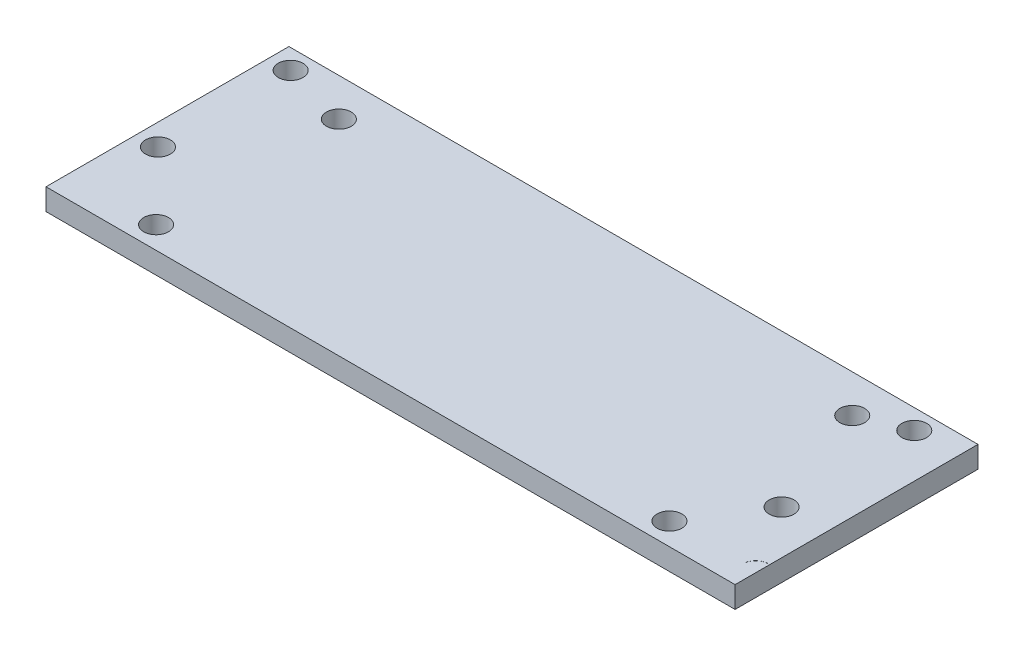
SolidWorks part; units mm, degrees
ref_plane "Front" through (0, 0, 0) normal (0, 0, 1) x (1, 0, 0)
ref_plane "Top" through (0, 0, 0) normal (0, 1, 0) x (1, 0, 0)
ref_plane "Right" through (0, 0, 0) normal (1, 0, 0) x (0, 0, -1)
sketch "Sketch1" plane through (0, 0, 0) normal (0, 1, 0) x (1, 0, 0)
  line L1 (57.15, -17.907) -> (-57.15, -17.907)
  line L2 (57.15, -17.907) -> (57.15, 17.907)
  line L3 (57.15, 17.907) -> (-57.15, 17.907)
  line L4 (-57.15, -17.907) -> (-57.15, 17.907)
  line L5 (57.15, -17.907) -> (-57.15, 17.907) construction
  line L6 (57.15, 17.907) -> (-57.15, -17.907) construction
  point P0 (0, 0)
  dimension "D1" = 35.814
  dimension "D2" = 114.3
extrude "Boss-Extrude1" add sketch "Sketch1" along normal blind 3.175
sketch "Sketch3" plane through (0, 3.175, 0) normal (0, 1, 0) x (1, 0, 0)
  line L0 (0, 17.907) -> (0, -17.907) construction
  line L1 (57.15, 17.907) -> (-57.15, 17.907) construction
  line L2 (-57.15, -17.907) -> (57.15, -17.907) construction
  line L3 (-37.592, 17.907) -> (-50.8, 17.907) construction
  line L4 (-50.8, 17.907) -> (-57.15, 17.907) construction
  line L5 (-53.975, 17.907) -> (-53.975, 14.986) construction
  line L6 (-53.975, 14.986) -> (-53.975, -4.572) construction
  line L7 (-50.8, 17.907) -> (-37.592, 17.907) construction
  line L8 (-44.196, 17.907) -> (-44.196, 12.319) construction
  line L9 (-44.196, 12.319) -> (-44.196, -14.6304) construction
  circle A0 centre (-53.975, 14.986) radius 1.8288
  circle A1 centre (-53.975, -4.572) radius 1.8288
  circle A2 centre (-44.196, 12.319) radius 1.8288
  circle A3 centre (-44.196, -14.6304) radius 1.8288
  circle A4 centre (44.196, -14.6304) radius 1.8288
  circle A5 centre (53.975, -4.572) radius 1.8288
  circle A6 centre (44.196, 12.319) radius 1.8288
  circle A7 centre (53.975, 14.986) radius 1.8288
  dimension "D3" = 3.6576
  dimension "D5" = 3.6576
  dimension "D7" = 3.6576
  dimension "D9" = 26.9494
  dimension "D10" = 3.6576
  dimension "D1" = 50.8
  dimension "D2" = 2.921
  dimension "D4" = 19.558
  dimension "D6" = 13.208
  dimension "D8" = 5.588
extrude "Cut-Extrude2" cut sketch "Sketch3" against normal through all
sketch "Sketch4" plane through (0, 3.175, 0) normal (0, 1, 0) x (1, 0, 0)
  line L0 (57.15, 17.907) -> (-57.15, 17.907) construction
  line L1 (57.15, -17.907) -> (44.45, -17.907)
  line L2 (57.15, -17.907) -> (57.15, 17.907)
  line L3 (57.15, 17.907) -> (44.45, 17.907)
  line L4 (44.45, -17.907) -> (44.45, 17.907)
  dimension "D1" = 12.7
extrude "Cut-Extrude3" cut sketch "Sketch4" against normal through all
sketch "Sketch5" plane through (0, 3.175, 0) normal (0, 1, 0) x (1, 0, 0)
  line L0 (-6.35, 17.907) -> (-6.35, -17.907) construction
  line L1 (44.45, 17.907) -> (-57.15, 17.907) construction
  line L2 (-57.15, -17.907) -> (44.45, -17.907) construction
  circle A0 centre (-44.196, 12.319) radius 1.8288
  circle A1 centre (-53.975, 14.986) radius 1.8288
  circle A2 centre (-53.975, -4.572) radius 1.8288
  circle A3 centre (-44.196, -14.6304) radius 1.8288
  circle A4 centre (31.496, -14.6304) radius 1.8288
  circle A5 centre (41.275, -4.572) radius 1.8288
  circle A6 centre (31.496, 12.319) radius 1.8288
  circle A7 centre (41.275, 14.986) radius 1.8288
extrude "Cut-Extrude4" cut sketch "Sketch5" against normal through all
sketch "Sketch6" plane through (0, 3.175, 0) normal (0, 1, 0) x (1, 0, 0)
  line L0 (44.196, -16.4592) -> (44.45, -16.7132)
  line L1 (44.45, -16.4415) -> (44.45, -17.907) construction
  line L2 (44.45, -16.7132) -> (44.45, -12.5512)
  line L3 (44.45, 10.5079) -> (44.45, -12.8193) construction
  line L4 (44.45, -12.5512) -> (44.196, -12.8016)
  line L5 (44.45, 10.5079) -> (44.45, 14.5425)
  line L6 (44.45, 17.907) -> (44.45, 14.1301) construction
  line L7 (44.45, 14.5425) -> (44.196, 14.1478)
  arc A0 (44.196, -16.4592) -> (44.196, -12.8016) centre (44.196, -14.6304) cw
  arc A1 (44.45, -12.8193) -> (44.45, -16.4415) centre (44.196, -14.6304) ccw construction
  arc A2 (44.45, 10.5079) -> (44.196, 14.1478) centre (44.196, 12.319) cw
  arc A3 (44.45, 14.1301) -> (44.45, 10.5079) centre (44.196, 12.319) ccw construction
sketch "Sketch8" plane through (0, 3.175, 0) normal (0, 1, 0) x (1, 0, 0)
  line L0 (44.196, -16.4592) -> (44.45, -16.7132) construction
  line L1 (44.196, 14.1478) -> (44.45, 14.5425)
  line L2 (44.45, 14.5425) -> (44.45, 10.5079)
  line L3 (44.196, -12.8016) -> (44.45, -12.5512)
  line L4 (44.45, -12.5512) -> (44.45, -16.7132)
  line L5 (44.45, -16.7132) -> (44.323, -16.5862)
  arc A0 (44.323, -16.5862) -> (44.196, -12.8016) centre (44.2595, -14.6939) cw
  arc A1 (44.45, 10.5079) -> (44.196, 14.1478) centre (44.196, 12.319) cw
extrude "Boss-Extrude4" add sketch "Sketch8" against normal blind 3.175
sketch "Sketch9" plane through (0, 3.175, 0) normal (0, 1, 0) x (1, 0, 0)
  line L0 (41.275, -4.572) -> (37.973, -4.572) construction
  line L1 (41.275, 14.986) -> (37.973, 14.986) construction
  circle A0 centre (37.973, -4.572) radius 1.8288
  circle A1 centre (37.973, 14.986) radius 1.8288
  dimension "D3" = 3.6576
  dimension "D4" = 3.6576
  dimension "D1" = 3.302
  dimension "D2" = 3.302
extrude "Cut-Extrude5" cut sketch "Sketch9" against normal through all
sketch "Sketch10" plane through (0, 3.175, 0) normal (0, 1, 0) x (1, 0, 0)
  arc A0 (39.624, 14.1994) -> (39.624, 15.7726) centre (37.973, 14.986) ccw
  arc A1 (39.624, -5.3586) -> (39.624, -3.7854) centre (37.973, -4.572) ccw
  arc A2 (39.624, 14.1994) -> (39.624, 15.7726) centre (41.275, 14.986) ccw
  arc A3 (39.624, -5.3586) -> (39.624, -3.7854) centre (41.275, -4.572) ccw
extrude "Boss-Extrude5" add sketch "Sketch10" against normal blind 3.175
